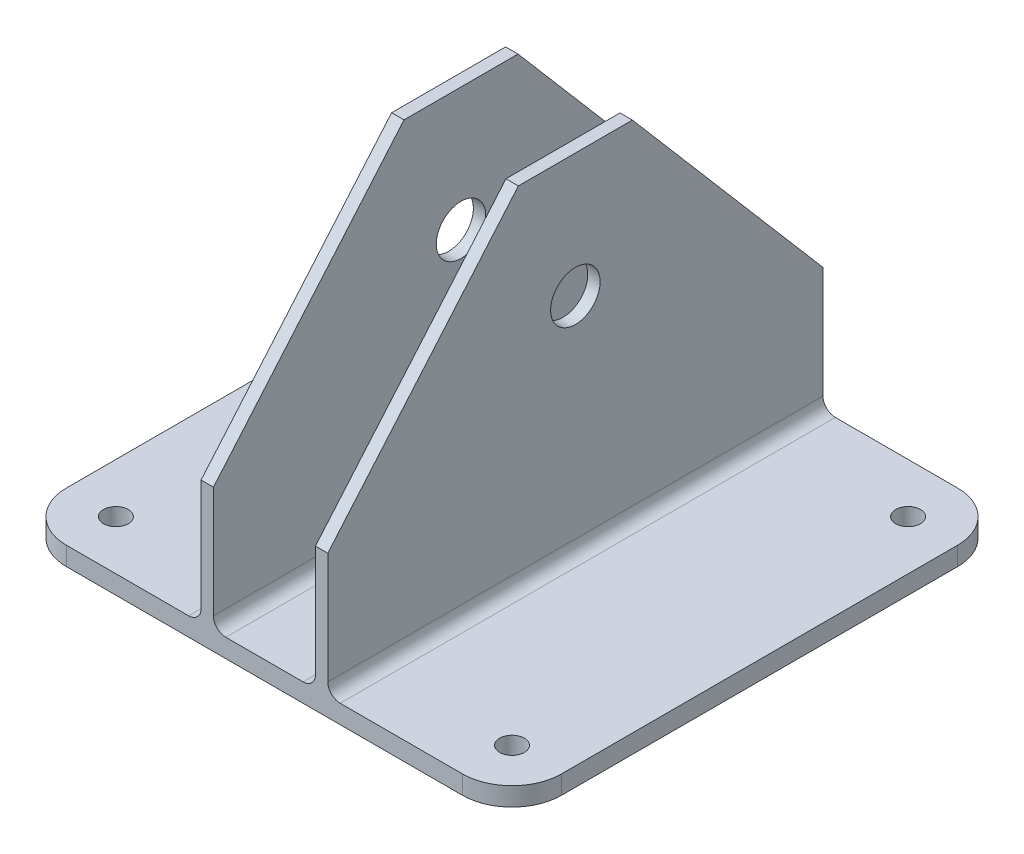
SolidWorks part; units mm, degrees
material "Alloy Steel"
ref_plane "Front Plane" through (0, 0, 0) normal (0, 0, 1) x (1, 0, 0)
ref_plane "Top Plane" through (0, 0, 0) normal (0, 1, 0) x (1, 0, 0)
ref_plane "Right Plane" through (0, 0, 0) normal (1, 0, 0) x (0, 0, -1)
sketch "Sketch1" plane through (0, 0, 0) normal (0, 1, 0) x (1, 0, 0)
  line L0 (0, 0) -> (63.5, 0) construction
  line L1 (-63.5, 63.5) -> (63.5, 63.5)
  line L2 (-63.5, 63.5) -> (-63.5, -63.5)
  line L3 (-63.5, -63.5) -> (63.5, -63.5)
  line L4 (63.5, 63.5) -> (63.5, -63.5)
  line L5 (63.5, 0) -> (0, 0) construction
  line L6 (0, 0) -> (-63.5, 0) construction
  line L7 (-63.5, 0) -> (0, 0) construction
  line L8 (0, 0) -> (0, 63.5) construction
  line L9 (0, 63.5) -> (0, 0) construction
  line L10 (0, 0) -> (0, -63.5) construction
  dimension "D1" = 127
  dimension "D2" = 127
extrude "Boss-Extrude1" add sketch "Sketch1" along normal blind 4.7625
sketch "Sketch2" plane through (0, 4.7625, 0) normal (0, 1, 0) x (1, 0, 0)
  line L0 (63.5, 63.5) -> (-63.5, 63.5) construction
  line L1 (-16.256, 63.5) -> (-13.081, 63.5)
  line L2 (-16.256, 63.5) -> (-16.256, -63.5)
  line L3 (-16.256, -63.5) -> (-13.081, -63.5)
  line L4 (-13.081, 63.5) -> (-13.081, -63.5)
  line L5 (-63.5, -63.5) -> (63.5, -63.5) construction
  line L6 (0, 152.4) -> (0, -63.5) construction
  line L7 (13.081, 63.5) -> (16.256, 63.5)
  line L8 (13.081, 63.5) -> (13.081, -63.5)
  line L9 (13.081, -63.5) -> (16.256, -63.5)
  line L10 (16.256, 63.5) -> (16.256, -63.5)
  point P15 (0, 44.45)
  dimension "D1" = 26.162
  dimension "D2" = 3.175
extrude "Boss-Extrude2" add sketch "Sketch2" along normal blind 88.9
sketch "Sketch3" plane through (-16.256, 0, 0) normal (-1, 0, 0) x (0, 0, 1)
  line L0 (-63.5, 61.9125) -> (63.5, 61.9125) construction
  line L3 (0, 93.6625) -> (0, 4.7625) construction
  line L4 (-63.5, 93.6625) -> (63.5, 93.6625) construction
  line L5 (-63.5, 4.7625) -> (63.5, 4.7625) construction
  line L7 (-63.5, 93.6625) -> (-63.5, 4.7625) construction
  line L8 (-63.5, 49.2125) -> (63.5, 49.2125) construction
  line L9 (63.5, 93.6625) -> (63.5, 4.7625) construction
  circle A0 centre (0, 61.9125) radius 6.35
  point P17 (0, 0)
  dimension "D1" = 12.7
  dimension "D2" = 31.75
extrude "Cut-Extrude1" cut sketch "Sketch3" against normal through all both and the other way through all
fillet "Fillet1" radius 3.175 4 edges at (16.256, 4.7625, 0) (13.081, 4.7625, 0) (-13.081, 4.7625, 0) (-16.256, 4.7625, 0)
sketch "Sketch4" plane through (0, 4.7625, 0) normal (0, 1, 0) x (1, 0, 0)
  line L0 (-63.5, 63.5) -> (-63.5, -63.5) construction
  line L1 (-19.431, 63.5) -> (-63.5, 63.5) construction
  line L2 (-63.5, 0) -> (63.5, 0) construction
  line L3 (63.5, -63.5) -> (63.5, 63.5) construction
  circle A0 centre (-50.8, 50.8) radius 3.175
  circle A1 centre (-50.8, -50.8) radius 3.175
  circle A2 centre (-50.8, 25.4) radius 3.175
  circle A3 centre (-50.8, 0) radius 3.175
  circle A4 centre (-50.8, -25.4) radius 3.175
  circle A5 centre (-50.8, -50.8) radius 3.175
  dimension "D1" = 6.35
  dimension "D3" = 12.7
  dimension "D2" = 12.7
  dimension "D4" = 5
sketch "Sketch5" plane through (0, 4.7625, 0) normal (0, 1, 0) x (1, 0, 0)
  line L0 (0, 63.5) -> (0, -63.5) construction
  line L1 (9.906, 63.5) -> (-9.906, 63.5) construction
  line L2 (-9.906, -63.5) -> (9.906, -63.5) construction
ref_plane "Plane1" through (0, 0, 0) normal (-1, 0, 0) x (0, 0, 1)
chamfer "Chamfer1" distance 25.4 4 edges at (14.6685, 93.6625, 63.5) (-14.6685, 93.6625, 63.5) (14.6685, 93.6625, -63.5) (-14.6685, 93.6625, -63.5)
extrude "Cut-Extrude4" cut sketch "Sketch4" against normal through all both and the other way through all contours A1 | A0
mirror "Mirror2" about plane through (0, 0, 0) normal (-1, 0, 0) of "Cut-Extrude4"
fillet "Fillet5" radius 12.7 4 edges at (63.5, 2.3813, -63.5) (63.5, 2.3813, 63.5) (-63.5, 2.3813, 63.5) (-63.5, 2.3813, -63.5)
sketch "Sketch6" plane through (16.256, 0, 0) normal (1, 0, 0) x (0, 0, -1)
  circle A0 centre (0, 61.9125) radius 6.35 construction
  circle A1 centre (0, 61.9125) radius 6.35
  circle A2 centre (0, 61.9125) radius 31.75 construction
  dimension "D1" = 25.4
sketch "Sketch7" plane through (-16.256, 0, 0) normal (-1, 0, 0) x (0, 0, 1)
  line L0 (-14.6243, 93.6625) -> (-63.5, 36.5125)
  line L1 (-38.1, 93.6625) -> (38.1, 93.6625) construction
  line L2 (-63.5, 68.2625) -> (-63.5, 7.9375) construction
  line L3 (0, 93.6625) -> (0, 0) construction
  line L4 (14.6243, 93.6625) -> (63.5, 36.5125)
  line L11 (63.5, 7.9375) -> (63.5, 68.2625)
  line L12 (63.5, 68.2625) -> (38.1, 93.6625)
  line L13 (38.1, 93.6625) -> (-38.1, 93.6625)
  line L14 (-38.1, 93.6625) -> (-63.5, 68.2625)
  line L15 (-63.5, 68.2625) -> (-63.5, 7.9375)
  line L16 (-63.5, 7.9375) -> (63.5, 7.9375)
  line L17 (63.5, 7.9375) -> (63.5, 68.2625)
  line L18 (63.5, 68.2625) -> (38.1, 93.6625)
  line L19 (38.1, 93.6625) -> (-38.1, 93.6625)
  line L20 (-38.1, 93.6625) -> (-63.5, 68.2625)
  line L21 (-63.5, 68.2625) -> (-63.5, 7.9375)
  line L22 (-63.5, 7.9375) -> (63.5, 7.9375)
  circle A1 centre (0, 61.9125) radius 31.75 construction
  point P14 (-63.5, 36.4773)
  line M4 (63.5, 7.9375) -> (63.5, 68.2625)
  line M5 (63.5, 68.2625) -> (38.1, 93.6625)
  line M6 (38.1, 93.6625) -> (-38.1, 93.6625)
  line M7 (-38.1, 93.6625) -> (-63.5, 68.2625)
  line M8 (-63.5, 68.2625) -> (-63.5, 7.9375)
  dimension "D1" = 28.575
  dimension "D2" = 0
extrude "Cut-Extrude5" cut sketch "Sketch7" against normal through all both and the other way through all contours L0 M6 M7 M8 | L4 M6 M4 M5
